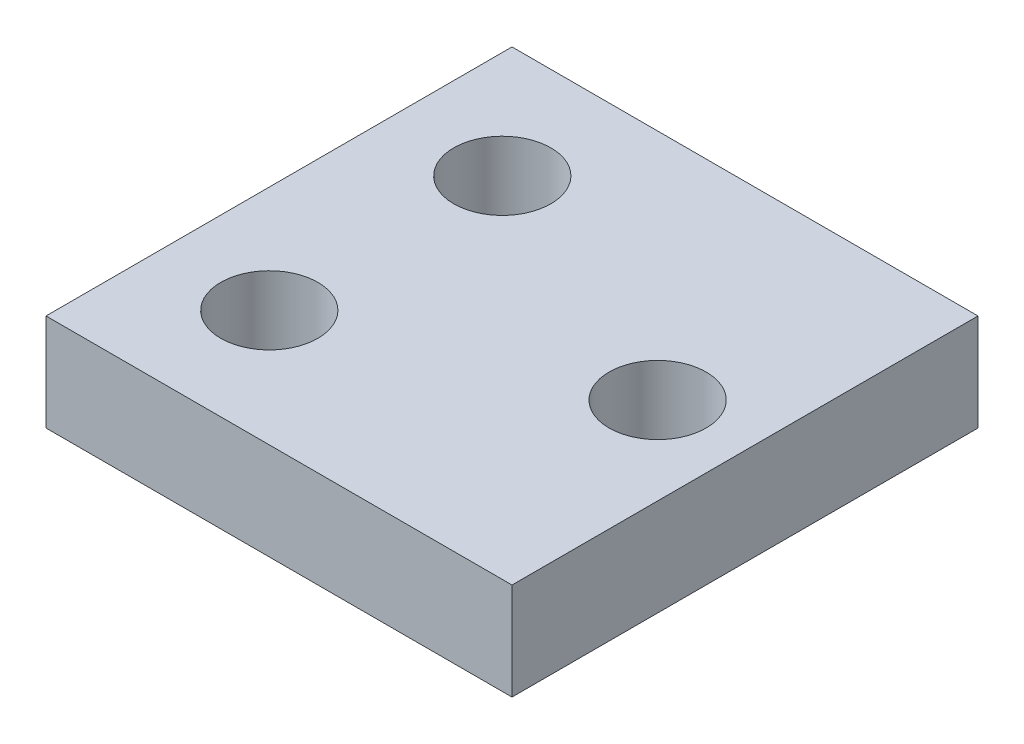
SolidWorks part; units mm, degrees
ref_plane "Front Plane" through (0, 0, 0) normal (0, 0, 1) x (1, 0, 0)
ref_plane "Top Plane" through (0, 0, 0) normal (0, 1, 0) x (1, 0, 0)
ref_plane "Right Plane" through (0, 0, 0) normal (1, 0, 0) x (0, 0, -1)
sketch "Sketch1" plane through (0, 0, 0) normal (0, 1, 0) x (1, 0, 0)
  line L1 (-15.24, 15.24) -> (15.24, 15.24)
  line L2 (-15.24, 15.24) -> (-15.24, -15.24)
  line L3 (-15.24, -15.24) -> (15.24, -15.24)
  line L4 (15.24, 15.24) -> (15.24, -15.24)
  dimension "D1" = 15.24
  dimension "D2" = 15.24
  dimension "D3" = 15.24
  dimension "D4" = 15.24
extrude "Boss-Extrude1" add sketch "Sketch1" along normal mid plane 6.35
sketch "Sketch2" plane through (0, 3.175, 0) normal (0, 1, 0) x (1, 0, 0)
  circle A0 centre (9.525, 0) radius 3.175
  circle A1 centre (-8.255, -7.62) radius 3.175
  circle A2 centre (-8.255, 7.62) radius 3.175
  dimension "D1" = 9.525
  dimension "D2" = 8.255
  dimension "D3" = 7.62
  dimension "D4" = 7.62
extrude "Cut-Extrude1" cut sketch "Sketch2" against normal up to next
